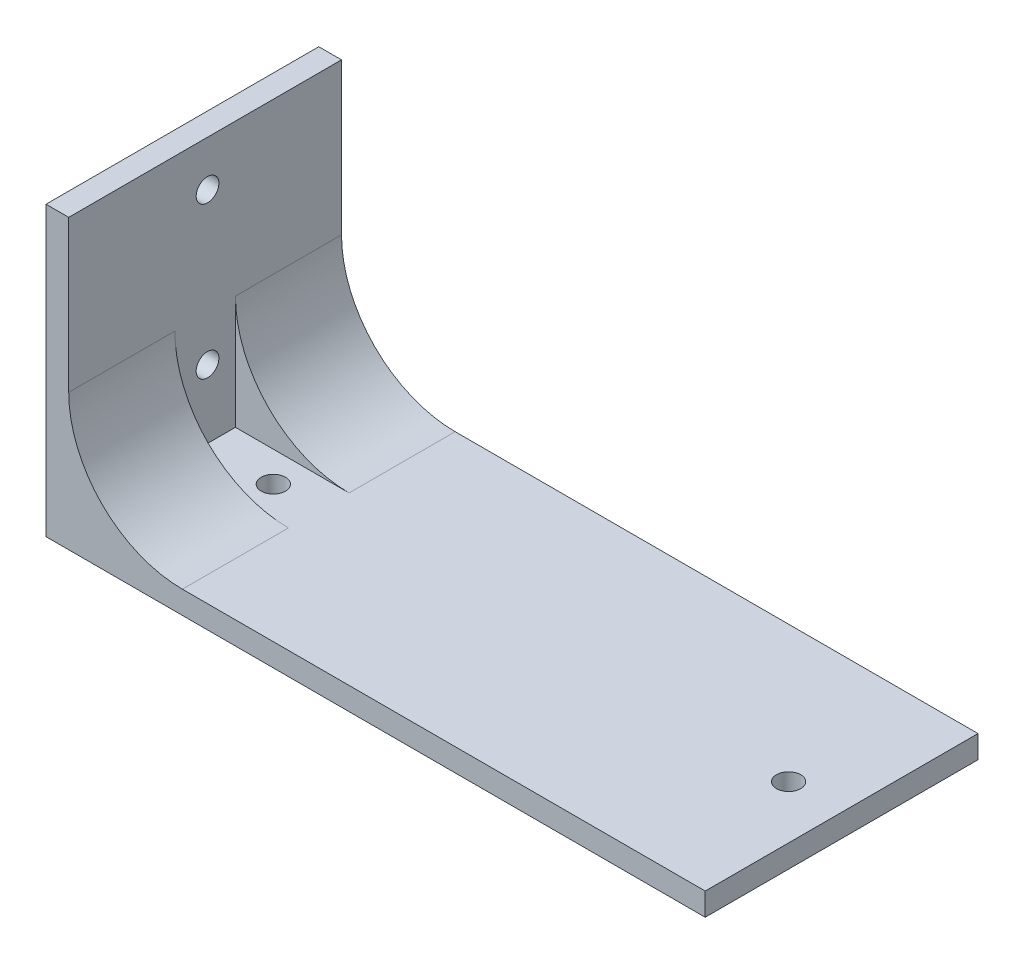
SolidWorks part; units mm, degrees
ref_plane "Front Plane" through (0, 0, 0) normal (0, 0, 1) x (1, 0, 0)
ref_plane "Top Plane" through (0, 0, 0) normal (0, 1, 0) x (1, 0, 0)
ref_plane "Right Plane" through (0, 0, 0) normal (1, 0, 0) x (0, 0, -1)
sketch "Sketch1" plane through (0, 0, 0) normal (0, 1, 0) x (1, 0, 0)
  line L0 (-33.2244, -4.6417) -> (53.7756, -4.6417) construction
  line L1 (-33.2244, 13.3583) -> (53.7756, 13.3583)
  line L2 (-33.2244, 13.3583) -> (-33.2244, -22.6417)
  line L3 (-33.2244, -22.6417) -> (53.7756, -22.6417)
  line L4 (53.7756, 13.3583) -> (53.7756, -22.6417)
  circle A0 centre (46.7756, -4.6417) radius 1.6
  circle A1 centre (-21.2244, -4.6417) radius 1.6
  dimension "D3" = 3.2
  dimension "D5" = 68
  dimension "D1" = 87
  dimension "D2" = 36
  dimension "D4" = 7
extrude "Boss-Extrude1" add sketch "Sketch1" along normal blind 3
sketch "Sketch2" plane through (0, 3, 0) normal (0, 1, 0) x (1, 0, 0)
  line L2 (-33.2244, 13.3583) -> (-30.2244, 13.3583)
  line L3 (-33.2244, 13.3583) -> (-33.2244, -0.6417)
  line L4 (-33.2244, -0.6417) -> (-30.2244, -0.6417)
  line L6 (-30.2244, 13.3583) -> (-30.2244, -0.6417)
  line L7 (-30.2244, -8.6417) -> (-33.2244, -8.6417)
  line L8 (-30.2244, -8.6417) -> (-30.2244, -22.6417)
  line L9 (-30.2244, -22.6417) -> (-33.2244, -22.6417)
  line L10 (-33.2244, -8.6417) -> (-33.2244, -22.6417)
  dimension "D1" = 3
  dimension "D2" = 3
  dimension "D3" = 14
  dimension "D4" = 14
extrude "Boss-Extrude2" add sketch "Sketch2" along normal blind 35
fillet "Fillet2" radius 15 2 edges at (-30.2244, 3, 15.6417) (-30.2244, 3, -6.3583)
sketch "Sketch3" plane through (0, 3, 0) normal (0, 1, 0) x (1, 0, 0)
  line L0 (-15.2244, -8.6417) -> (-33.2244, -8.6417) construction
  line L1 (-33.2244, -0.6417) -> (-30.2244, -0.6417)
  line L2 (-33.2244, -0.6417) -> (-33.2244, -8.6417)
  line L3 (-33.2244, -8.6417) -> (-30.2244, -8.6417)
  line L4 (-30.2244, -0.6417) -> (-30.2244, -8.6417)
  dimension "D1" = 3
extrude "Boss-Extrude3" add sketch "Sketch3" along normal blind 35
sketch "Sketch4" plane through (-30.2244, 0, 0) normal (1, 0, 0) x (0, 0, -1)
  line L0 (-4.3245, 12) -> (-4.3245, 32) construction
  line L1 (-22.6417, 38) -> (13.3583, 38) construction
  circle A0 centre (-4.3245, 32) radius 1.5
  circle A1 centre (-4.3245, 12) radius 1.5
  dimension "D2" = 3
  dimension "D1" = 20
  dimension "D3" = 6
extrude "Cut-Extrude1" cut sketch "Sketch4" against normal blind 30
